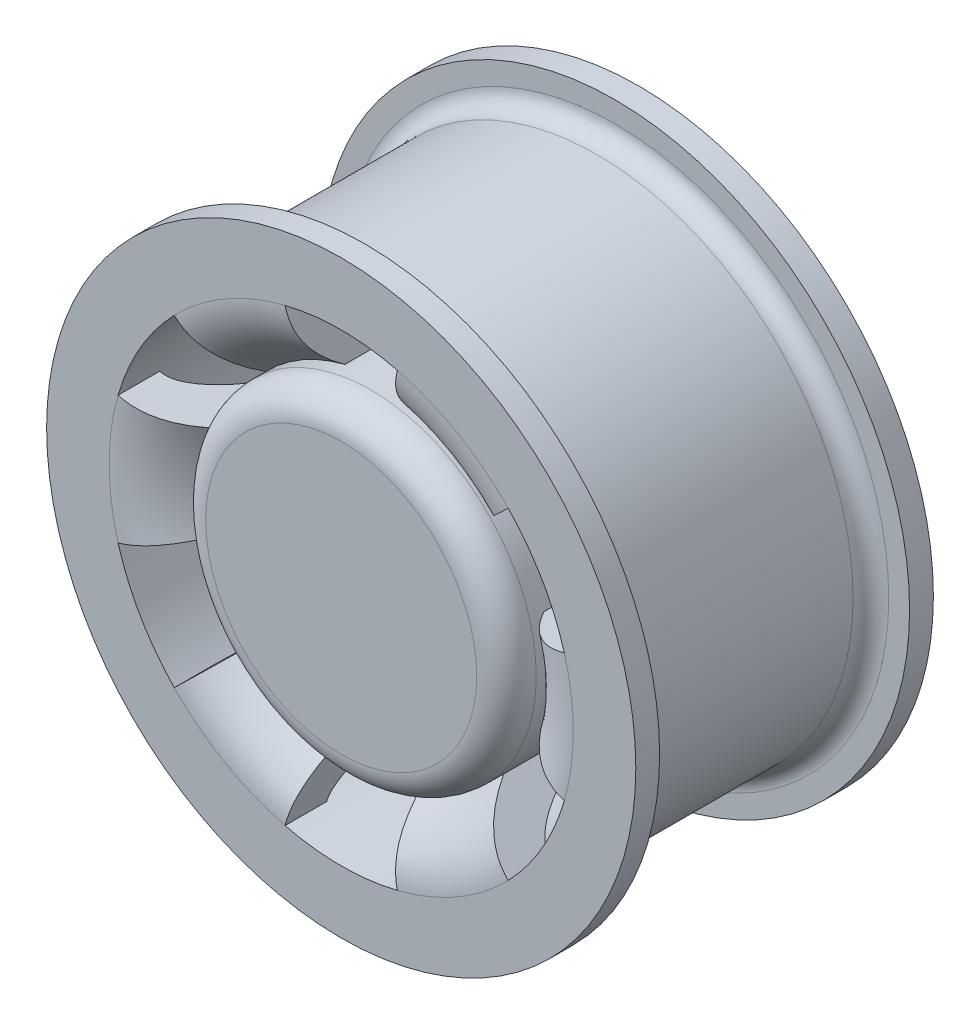
SolidWorks part; units mm, degrees
material "ABS"
ref_plane "Спереди" through (0, 0, 0) normal (0, 0, 1) x (1, 0, 0)
ref_plane "Сверху" through (0, 0, 0) normal (0, 1, 0) x (1, 0, 0)
ref_plane "Справа" through (0, 0, 0) normal (1, 0, 0) x (0, 0, -1)
sketch "Эскиз1" plane through (0, 0, 0) normal (0, 1, 0) x (1, 0, 0)
  line L0 (0, 0) -> (0, 47.4199) construction
  line L1 (0, 0) -> (79.812, 0) construction
  line L2 (39, 25) -> (39, -18)
  line L3 (39, -25) -> (47, -25)
  line L5 (49.5, -21) -> (46, -21)
  line L6 (43, -18) -> (43, 18)
  line L9 (39, 25) -> (47, 25)
  line L10 (40.0579, -25) -> (51.9421, -25) construction
  line L11 (20.5, 0) -> (27.7696, 0)
  line L13 (47, -25) -> (49.5, -25)
  line L14 (49.5, -25) -> (49.5, -21)
  line L15 (46, 21) -> (49.5, 21)
  line L16 (49.5, 21) -> (49.5, 25)
  line L17 (49.5, 25) -> (47, 25)
  arc A0 (46, -21) -> (43, -18) centre (46, -18) cw
  arc A1 (46, 21) -> (43, 18) centre (46, 18) ccw
  spline S0 degree 3 poles (39, -25) (27.4862, -25) (22.2386, -6.3236) (20.5, 0) knots 0 0 0 0 1 1 1 1
  spline S1 degree 1 poles (39, -18) (27.2495, 1.8557) knots 0 0 1 1 construction
  spline S2 degree 3 poles (39, -18) (38.7744, -18) (38.3151, -17.9532) (37.6952, -17.7601) (36.9533, -17.3777) (35.803, -16.5242) (34.1483, -14.7283) (32.1952, -11.6157) (30.4751, -7.9745) (29.2989, -4.8534) (28.5209, -2.5054) (28.0174, -0.8635) (27.6637, 0.3644) (27.4146, 1.2563) (27.3057, 1.6516) (27.2495, 1.8557) knots 0 0 0 0 0.0625 0.125 0.1875 0.25 0.375 0.5 0.625 0.75 0.8125 0.875 0.9375 0.96875 1 1 1 1 only from (39, -18) to (27.7696, 0)
  point P3 (43, 21)
  point P12 (43, -21)
  point P16 (43, 0)
  point P19 (39.005, 0)
  dimension "D5" = 3
  dimension "D1" = 25
  dimension "D2" = 8
  dimension "D3" = 3.5
  dimension "D4" = 4
  dimension "D6" = 43
  dimension "D7" = 20.5
  dimension "D8" = 28
  dimension "D10" = 18
  dimension "D11" = 7.2696
  dimension "D12" = 4
  dimension "D13" = 3.5
  dimension "D9" = 7
revolve "Повернуть1" add sketch "Эскиз1" angle 360 about L0
sketch "Эскиз2" plane through (0, 0, 0) normal (0, 0, -1) x (-1, 0, 0)
  circle A0 centre (0, 0) radius 20.5 construction
  circle A1 centre (0, 0) radius 27.7696 construction
  circle A2 centre (0, 0) radius 20.5
  circle A3 centre (0, 0) radius 27.7696
extrude "Бобышка-Вытянуть1" add sketch "Эскиз2" against normal through all
sketch "Эскиз3" plane through (0, 0, 25) normal (0, 0, 1) x (1, 0, 0)
  circle A0 centre (0, 0) radius 27.7696 construction
  circle A1 centre (0, 0) radius 27.7696
extrude "Бобышка-Вытянуть2" add sketch "Эскиз3" against normal blind 5
sketch "Эскиз4" plane through (0, 0, 25) normal (0, 0, 1) x (1, 0, 0)
  line L0 (-6.7181, 26.9447) -> (-9.435, 37.8415)
  line L1 (6.7181, 26.9447) -> (9.435, 37.8415)
  circle A0 centre (0, 0) radius 27.7696 construction
  arc A1 (6.7181, 26.9447) -> (-6.7181, 26.9447) centre (0, 0) ccw
  circle A2 centre (0, 0) radius 39 construction
  arc A3 (9.435, 37.8415) -> (-9.435, 37.8415) centre (0, 0) ccw
  dimension "D1" = 28
extrude "Вырез-Вытянуть1" cut sketch "Эскиз4" against normal through all
pattern_circular "Круговой массив1" count 6 over 360 about axis through (0, 0, 0) along (0, 0, 1) of "Вырез-Вытянуть1"
fillet "Скругление1" radius 5 1 edges at (-27.7696, 0, 25)
sketch3d "Трехмерный эскиз1"
  line L0 (0, 0, 0) -> (-27.7696, 0, 0) construction
  arc A0 (-26.6938, 7.6543, 0) -> (-26.6938, -7.6543, 0) centre (0, 0, 0) ccw construction
  point P6 (0, 0, 27.7696)
  point P7 (-23.75, 0, 0)
  dimension "D1" = 23.75
hole_wizard "Сверление под метчик M51" positions "Эскиз11" profile "Эскиз13" hole size "M5" standard "ISO"
sketch "Эскиз11" plane through (0, 0, 0) normal (0, 0, -1) x (-1, 0, 0)
  point P0 (23.75, 0)
sketch "Эскиз13" plane through (-23.75, 0, 0) normal (1, 0, 0) x (0, 1, 0)
  line L0 (0, 0) -> (0, 23.2618)
  line L1 (0, 23.2618) -> (2.1, 22)
  line L2 (2.1, 22) -> (2.1, 0)
  line L5 (2.1, 0) -> (0, 0)
  line L10 (0, 23.2618) -> (-2.1, 22) construction
  line L11 (0, -6.35) -> (0, 107.95) construction
  dimension "Диаметр отверстия" = 4.2
  dimension "Глубина отверстия" = 22
  dimension "Угол заточки сверла" = 118
cosmetic thread "Условное изображение резьбы1" parameters "D2"=5
pattern_circular "Круговой массив3" count 6 over 360 about axis through (0, 0, 0) along (0, 0, 1) of "Сверление под метчик M51"
chamfer "Фаска2" distance 0.6 angle 45 6 edges at (-13.975, -20.5681, 0) (9.775, -20.5681, 0) (21.65, 0, 0) (9.775, 20.5681, 0) (-13.975, 20.5681, 0) (-25.85, 0, 0)
